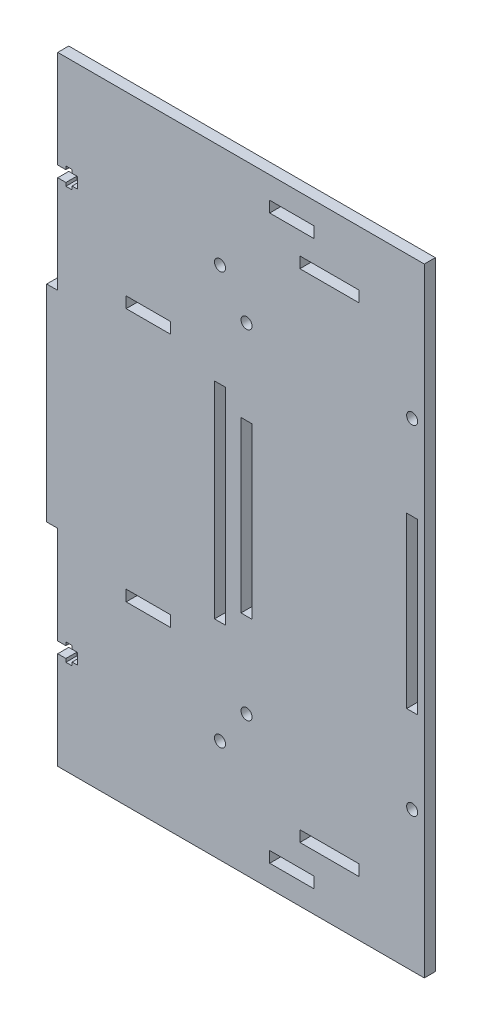
SolidWorks part; units mm, degrees
ref_plane "Alzado" through (0, 0, 0) normal (0, 0, 1) x (1, 0, 0)
ref_plane "Planta" through (0, 0, 0) normal (0, 1, 0) x (1, 0, 0)
ref_plane "Vista lateral" through (0, 0, 0) normal (1, 0, 0) x (0, 0, -1)
sketch "Croquis1" plane through (0, 0, 0) normal (0, 0, 1) x (1, 0, 0)
  line L0 (68, 280) -> (68, 236.7398) construction
  line L1 (0, 0) -> (136, 0)
  line L2 (0, 0) -> (0, 280)
  line L3 (0, 280) -> (136, 280)
  line L4 (136, 0) -> (136, 280)
  line L5 (0, 280) -> (5, 280)
  line L6 (0, 280) -> (0, 0)
  line L7 (0, 0) -> (5, 0)
  line L8 (5, 280) -> (5, 0)
  line L9 (131, 280) -> (131, 0)
  line L10 (0, 186.6667) -> (5, 186.6667)
  line L11 (5, 93.3333) -> (0, 93.3333)
  line L12 (131, 93.3333) -> (136, 93.3333)
  line L13 (136, 186.6667) -> (131, 186.6667)
  line L14 (0, 140) -> (16.4555, 140) construction
  dimension "D1" = 280
  dimension "D2" = 136
  dimension "D3" = 5
  dimension "D4" = 93.3333
  dimension "D5" = 93.3333
extrude "Saliente-Extruir1" add sketch "Croquis1" along normal blind 5 contours L9 L3 L8 L1 | L11 L8 L10 L6
sketch "Croquis2" plane through (0, 0, 5) normal (0, 0, 1) x (1, 0, 0)
  line L0 (5, 233.3333) -> (14, 233.3333) construction
  line L1 (5, 280) -> (5, 186.6667) construction
  line L2 (68, 280) -> (68, 267.6992)
  line L3 (5, 280) -> (131, 280) construction
  line L4 (0, 140) -> (9.7749, 140)
  line L5 (0, 93.3333) -> (0, 186.6667) construction
  line L6 (5, 235.8333) -> (8.7, 235.8333)
  line L7 (8.7, 235.8333) -> (8.7, 237.3333)
  line L8 (8.7, 237.3333) -> (11.5, 237.3333)
  line L9 (11.5, 237.3333) -> (11.5, 235.8333)
  line L10 (11.5, 235.8333) -> (14, 235.8333)
  line L11 (14, 235.8333) -> (14, 230.8333)
  line L12 (11.5, 230.8333) -> (14, 230.8333)
  line L13 (11.5, 229.3333) -> (11.5, 230.8333)
  line L14 (8.7, 229.3333) -> (11.5, 229.3333)
  line L15 (8.7, 230.8333) -> (8.7, 229.3333)
  line L16 (5, 230.8333) -> (8.7, 230.8333)
  line L17 (131, 233.3333) -> (122, 233.3333) construction
  line L18 (131, 230.8333) -> (127.3, 230.8333)
  line L19 (127.3, 230.8333) -> (127.3, 229.3333)
  line L20 (127.3, 229.3333) -> (124.5, 229.3333)
  line L21 (124.5, 229.3333) -> (124.5, 230.8333)
  line L22 (124.5, 230.8333) -> (122, 230.8333)
  line L23 (122, 235.8333) -> (122, 230.8333)
  line L24 (124.5, 235.8333) -> (122, 235.8333)
  line L25 (124.5, 237.3333) -> (124.5, 235.8333)
  line L26 (127.3, 237.3333) -> (124.5, 237.3333)
  line L27 (127.3, 235.8333) -> (127.3, 237.3333)
  line L28 (131, 235.8333) -> (127.3, 235.8333)
  line L29 (131, 46.6667) -> (122, 46.6667) construction
  line L30 (5, 46.6667) -> (14, 46.6667) construction
  line L31 (131, 44.1667) -> (127.3, 44.1667)
  line L32 (127.3, 44.1667) -> (127.3, 42.6667)
  line L33 (127.3, 42.6667) -> (124.5, 42.6667)
  line L34 (124.5, 42.6667) -> (124.5, 44.1667)
  line L35 (124.5, 44.1667) -> (122, 44.1667)
  line L36 (122, 44.1667) -> (122, 49.1667)
  line L37 (124.5, 49.1667) -> (122, 49.1667)
  line L38 (124.5, 50.6667) -> (124.5, 49.1667)
  line L39 (127.3, 50.6667) -> (124.5, 50.6667)
  line L40 (127.3, 49.1667) -> (127.3, 50.6667)
  line L41 (131, 49.1667) -> (127.3, 49.1667)
  line L42 (5, 49.1667) -> (8.7, 49.1667)
  line L43 (8.7, 49.1667) -> (8.7, 50.6667)
  line L44 (8.7, 50.6667) -> (11.5, 50.6667)
  line L45 (11.5, 50.6667) -> (11.5, 49.1667)
  line L46 (11.5, 49.1667) -> (14, 49.1667)
  line L47 (14, 44.1667) -> (14, 49.1667)
  line L48 (11.5, 44.1667) -> (14, 44.1667)
  line L49 (11.5, 42.6667) -> (11.5, 44.1667)
  line L50 (8.7, 42.6667) -> (11.5, 42.6667)
  line L51 (8.7, 44.1667) -> (8.7, 42.6667)
  line L52 (5, 44.1667) -> (8.7, 44.1667)
  line M12 (5, 280) -> (5, 186.6667)
  line M16 (5, 93.3333) -> (5, 0)
  dimension "D1" = 2.5
  dimension "D2" = 4
  dimension "D3" = 2.8
  dimension "D4" = 9
  dimension "D5" = 3.7
extrude "Cortar-Extruir1" cut sketch "Croquis2" against normal blind 5 contours L16 L15 L14 L13 L12 L11 L10 L9 L8 L7 L6 M12 | L52 L51 L50 L49 L48 L47 L46 L45 L44 L43 L42 M16
sketch "Croquis3" plane through (0, 0, 5) normal (0, 0, 1) x (1, 0, 0)
  line L0 (5, 280) -> (131, 280) construction
  line L1 (76, 280) -> (81, 280)
  line L2 (76, 280) -> (76, 0)
  line L3 (76, 0) -> (81, 0)
  line L4 (81, 280) -> (81, 0)
  line L5 (5, 0) -> (131, 0) construction
  line L6 (5, 280) -> (5, 235.8333) construction
  line L7 (76, 186.6667) -> (81, 186.6667)
  line L8 (76, 93.3333) -> (81, 93.3333)
  point P10 (5, 257.9167)
  point P13 (78.5, 186.6667)
  dimension "D1" = 71
  dimension "D2" = 5
  dimension "D3" = 93.3333
  dimension "D4" = 93.3333
extrude "Cortar-Extruir2" cut sketch "Croquis3" against normal blind 5 contours L2 L8 L4 L7
sketch "Croquis4" plane through (0, 0, 5) normal (0, 0, 1) x (1, 0, 0)
  line L0 (78.5, 186.6667) -> (78.5, 280) construction
  line L1 (76, 186.6667) -> (81, 186.6667) construction
  line L2 (5, 280) -> (131, 280) construction
  line L3 (78.5, 93.3333) -> (78.5, 0) construction
  line L5 (76, 93.3333) -> (81, 93.3333) construction
  line L6 (5, 0) -> (131, 0) construction
  circle A0 centre (78.5, 233.3333) radius 2.5
  circle A1 centre (78.5, 46.6667) radius 2.5
  dimension "D1" = 5
extrude "Cortar-Extruir3" cut sketch "Croquis4" against normal blind 5
sketch "Croquis5" plane through (0, 0, 5) normal (0, 0, 1) x (1, 0, 0)
  line L0 (76, 280) -> (76, 0) construction
  line L1 (76, 186.6667) -> (76, 93.3333) construction
  line L2 (5, 0) -> (131, 0) construction
  line L3 (76, 140) -> (83.8361, 140) construction
  line L4 (76, 200) -> (36, 200)
  line L5 (76, 200) -> (76, 195)
  line L6 (76, 195) -> (36, 195)
  line L7 (36, 200) -> (36, 195)
  line L8 (0, 93.3333) -> (0, 186.6667) construction
  line L9 (76, 270) -> (121, 270)
  line L10 (76, 270) -> (76, 265)
  line L11 (76, 265) -> (121, 265)
  line L12 (121, 270) -> (121, 265)
  line L13 (56, 195) -> (56, 200)
  line L14 (101, 270) -> (101, 265)
  line L15 (101, 10) -> (101, 15)
  line L16 (56, 85) -> (56, 80)
  line L17 (121, 10) -> (121, 15)
  line L18 (76, 15) -> (121, 15)
  line L19 (76, 10) -> (76, 15)
  line L20 (76, 10) -> (121, 10)
  line L21 (36, 80) -> (36, 85)
  line L22 (76, 85) -> (36, 85)
  line L23 (76, 80) -> (76, 85)
  line L24 (76, 80) -> (36, 80)
  point P7 (76, 140)
  point P21 (0, 140)
  point P24 (101, 267.5)
  dimension "D1" = 5
  dimension "D2" = 5
  dimension "D3" = 60
  dimension "D4" = 45
  dimension "D5" = 40
  dimension "D6" = 70
  dimension "D7" = 20
extrude "Cortar-Extruir4" cut sketch "Croquis5" against normal blind 5
sketch "Croquis6" plane through (0, 0, 5) normal (0, 0, 1) x (1, 0, 0)
  line L0 (5, 0) -> (131, 0) construction
  line L1 (131, 280) -> (171, 280)
  line L2 (131, 280) -> (131, 0)
  line L3 (131, 0) -> (171, 0)
  line L4 (171, 280) -> (171, 0)
  dimension "D1" = 40
extrude "Saliente-Extruir2" add sketch "Croquis6" against normal blind 5
sketch "Croquis7" plane through (0, 0, 5) normal (0, 0, 1) x (1, 0, 0)
  line L0 (93, 250) -> (93, 30)
  line L1 (93, 30) -> (163, 30)
  line L2 (163, 30) -> (163, 250)
  line L3 (163, 250) -> (93, 250)
  line L4 (88, 255) -> (88, 25)
  line L5 (88, 25) -> (168, 25)
  line L6 (168, 25) -> (168, 255)
  line L7 (168, 255) -> (88, 255)
  line L8 (5, 0) -> (171, 0) construction
  line L9 (81, 186.6667) -> (81, 93.3333) construction
  line L10 (93, 250) -> (93, 255)
  line L11 (93, 30) -> (93, 25)
  line L12 (163, 30) -> (163, 25)
  line L13 (163, 250) -> (163, 255)
  line L14 (5, 280) -> (171, 280) construction
  line L16 (88, 178.3333) -> (93, 178.3333)
  line L17 (93, 101.6667) -> (88, 101.6667)
  line L18 (163, 178.3333) -> (168, 178.3333)
  line L19 (163, 101.6667) -> (168, 101.6667)
  line L20 (88, 216.6667) -> (93, 216.6667) construction
  line L21 (128, 255) -> (128, 151.4654) construction
  line L22 (163, 140) -> (153.4822, 140) construction
  line L23 (114.6667, 255) -> (114.6667, 250)
  line L24 (141.3333, 255) -> (141.3333, 250)
  line L25 (141.3333, 25) -> (141.3333, 30)
  line L26 (114.6667, 25) -> (114.6667, 30)
  circle A0 centre (90.5, 216.6667) radius 2.5
  circle A1 centre (165.5, 216.6667) radius 2.5
  circle A2 centre (165.5, 63.3333) radius 2.5
  circle A3 centre (90.5, 63.3333) radius 2.5
  dimension "D9" = 5
  dimension "D2" = 70
  dimension "D4" = 30
  dimension "D5" = 12
  dimension "D6" = 76.6667
  dimension "D7" = 76.6667
  dimension "D8" = 38.3333
  dimension "D10" = 26.6667
  dimension "D11" = 26.6667
  dimension "D12" = 30
  dimension "D3" = 5
extrude "Cortar-Extruir5" cut sketch "Croquis7" against normal blind 5 contours L17 L0 L16 L4 | L2 L19 L6 L18 | L26 L5 L25 L1 | L24 L7 L23 L3 | A0 | A1 | A2 | A3
sketch "Croquis8" plane through (0, 0, 5) normal (0, 0, 1) x (1, 0, 0)
  line L0 (101, 10) -> (121, 10) construction
  line L1 (121, 10) -> (121, 15) construction
  line L2 (101, 15) -> (121, 15) construction
  line L3 (101, 10) -> (101, 15) construction
  line L4 (141.3333, 25) -> (141.3333, 30) construction
  line L5 (114.6667, 25) -> (141.3333, 25) construction
  line L6 (114.6667, 25) -> (114.6667, 30) construction
  line L7 (114.6667, 30) -> (141.3333, 30) construction
  line L8 (163, 101.6667) -> (168, 101.6667) construction
  line L9 (168, 101.6667) -> (168, 178.3333) construction
  line L10 (163, 178.3333) -> (168, 178.3333) construction
  line L11 (163, 101.6667) -> (163, 178.3333) construction
  line L12 (88, 178.3333) -> (93, 178.3333) construction
  line L13 (93, 178.3333) -> (93, 101.6667) construction
  line L14 (93, 101.6667) -> (88, 101.6667) construction
  line L15 (88, 178.3333) -> (88, 101.6667) construction
  line L16 (76, 93.3333) -> (81, 93.3333) construction
  line L17 (76, 186.6667) -> (81, 186.6667) construction
  line L18 (81, 186.6667) -> (81, 93.3333) construction
  line L19 (76, 186.6667) -> (76, 93.3333) construction
  line L20 (56, 85) -> (56, 80) construction
  line L21 (36, 80) -> (36, 85) construction
  line L22 (56, 80) -> (36, 80) construction
  line L23 (56, 85) -> (36, 85) construction
  line L24 (101, 270) -> (101, 265) construction
  line L25 (101, 270) -> (121, 270) construction
  line L26 (121, 270) -> (121, 265) construction
  line L27 (101, 265) -> (121, 265) construction
  line L28 (141.3333, 255) -> (141.3333, 250) construction
  line L29 (141.3333, 250) -> (114.6667, 250) construction
  line L30 (141.3333, 255) -> (114.6667, 255) construction
  line L31 (114.6667, 255) -> (114.6667, 250) construction
  line L32 (5, 93.3333) -> (5, 49.1667)
  line L33 (5, 49.1667) -> (8.7, 49.1667)
  line L34 (8.7, 49.1667) -> (8.7, 50.6667)
  line L35 (8.7, 50.6667) -> (11.5, 50.6667)
  line L36 (11.5, 50.6667) -> (11.5, 49.1667)
  line L37 (11.5, 49.1667) -> (14, 49.1667)
  line L38 (14, 49.1667) -> (14, 44.1667)
  line L39 (14, 44.1667) -> (11.5, 44.1667)
  line L40 (11.5, 44.1667) -> (11.5, 42.6667)
  line L41 (11.5, 42.6667) -> (8.7, 42.6667)
  line L42 (8.7, 42.6667) -> (8.7, 44.1667)
  line L43 (8.7, 44.1667) -> (5, 44.1667)
  line L44 (5, 44.1667) -> (5, 0)
  line L45 (5, 0) -> (171, 0)
  line L46 (171, 0) -> (171, 280)
  line L47 (171, 280) -> (5, 280)
  line L48 (5, 280) -> (5, 235.8333)
  line L49 (5, 235.8333) -> (8.7, 235.8333)
  line L50 (8.7, 235.8333) -> (8.7, 237.3333)
  line L51 (8.7, 237.3333) -> (11.5, 237.3333)
  line L52 (11.5, 237.3333) -> (11.5, 235.8333)
  line L53 (11.5, 235.8333) -> (14, 235.8333)
  line L54 (14, 235.8333) -> (14, 230.8333)
  line L55 (14, 230.8333) -> (11.5, 230.8333)
  line L56 (11.5, 230.8333) -> (11.5, 229.3333)
  line L57 (11.5, 229.3333) -> (8.7, 229.3333)
  line L58 (8.7, 229.3333) -> (8.7, 230.8333)
  line L59 (8.7, 230.8333) -> (5, 230.8333)
  line L60 (5, 230.8333) -> (5, 186.6667)
  line L61 (5, 186.6667) -> (0, 186.6667)
  line L62 (0, 186.6667) -> (0, 93.3333)
  line L63 (0, 93.3333) -> (5, 93.3333)
  line L64 (5, 93.3333) -> (5, 49.1667)
  line L65 (5, 49.1667) -> (8.7, 49.1667)
  line L66 (8.7, 49.1667) -> (8.7, 50.6667)
  line L67 (8.7, 50.6667) -> (11.5, 50.6667)
  line L68 (11.5, 50.6667) -> (11.5, 49.1667)
  line L69 (11.5, 49.1667) -> (14, 49.1667)
  line L70 (14, 49.1667) -> (14, 44.1667)
  line L71 (14, 44.1667) -> (11.5, 44.1667)
  line L72 (11.5, 44.1667) -> (11.5, 42.6667)
  line L73 (11.5, 42.6667) -> (8.7, 42.6667)
  line L74 (8.7, 42.6667) -> (8.7, 44.1667)
  line L75 (8.7, 44.1667) -> (5, 44.1667)
  line L76 (5, 44.1667) -> (5, 0)
  line L77 (5, 0) -> (171, 0)
  line L78 (171, 0) -> (171, 280)
  line L79 (171, 280) -> (5, 280)
  line L80 (5, 280) -> (5, 235.8333)
  line L81 (5, 235.8333) -> (8.7, 235.8333)
  line L82 (8.7, 235.8333) -> (8.7, 237.3333)
  line L83 (8.7, 237.3333) -> (11.5, 237.3333)
  line L84 (11.5, 237.3333) -> (11.5, 235.8333)
  line L85 (11.5, 235.8333) -> (14, 235.8333)
  line L86 (14, 235.8333) -> (14, 230.8333)
  line L87 (14, 230.8333) -> (11.5, 230.8333)
  line L88 (11.5, 230.8333) -> (11.5, 229.3333)
  line L89 (11.5, 229.3333) -> (8.7, 229.3333)
  line L90 (8.7, 229.3333) -> (8.7, 230.8333)
  line L91 (8.7, 230.8333) -> (5, 230.8333)
  line L92 (5, 230.8333) -> (5, 186.6667)
  line L93 (5, 186.6667) -> (0, 186.6667)
  line L94 (0, 186.6667) -> (0, 93.3333)
  line L95 (0, 93.3333) -> (5, 93.3333)
  line L96 (56, 195) -> (56, 200) construction
  line L97 (56, 195) -> (36, 195) construction
  line L98 (36, 200) -> (36, 195) construction
  line L99 (56, 200) -> (36, 200) construction
  line L100 (101, 10) -> (121, 10)
  line L101 (121, 10) -> (121, 15)
  line L102 (101, 15) -> (121, 15)
  line L103 (101, 10) -> (101, 15)
  line L104 (141.3333, 25) -> (141.3333, 30)
  line L105 (114.6667, 25) -> (141.3333, 25)
  line L106 (114.6667, 25) -> (114.6667, 30)
  line L107 (114.6667, 30) -> (141.3333, 30)
  line L108 (163, 101.6667) -> (168, 101.6667)
  line L109 (168, 101.6667) -> (168, 178.3333)
  line L110 (163, 178.3333) -> (168, 178.3333)
  line L111 (163, 101.6667) -> (163, 178.3333)
  line L112 (88, 178.3333) -> (93, 178.3333)
  line L113 (93, 178.3333) -> (93, 101.6667)
  line L114 (93, 101.6667) -> (88, 101.6667)
  line L115 (88, 178.3333) -> (88, 101.6667)
  line L116 (76, 93.3333) -> (81, 93.3333)
  line L117 (76, 186.6667) -> (81, 186.6667)
  line L118 (81, 186.6667) -> (81, 93.3333)
  line L119 (76, 186.6667) -> (76, 93.3333)
  line L120 (56, 85) -> (56, 80)
  line L121 (36, 80) -> (36, 85)
  line L122 (56, 80) -> (36, 80)
  line L123 (56, 85) -> (36, 85)
  line L124 (101, 270) -> (101, 265)
  line L125 (101, 270) -> (121, 270)
  line L126 (121, 270) -> (121, 265)
  line L127 (101, 265) -> (121, 265)
  line L128 (141.3333, 255) -> (141.3333, 250)
  line L129 (141.3333, 250) -> (114.6667, 250)
  line L130 (141.3333, 255) -> (114.6667, 255)
  line L131 (114.6667, 255) -> (114.6667, 250)
  line L132 (56, 195) -> (56, 200)
  line L133 (56, 195) -> (36, 195)
  line L134 (36, 200) -> (36, 195)
  line L135 (56, 200) -> (36, 200)
  circle A0 centre (165.5, 63.3333) radius 2.5 construction
  circle A1 centre (90.5, 63.3333) radius 2.5 construction
  circle A2 centre (78.5, 46.6667) radius 2.5 construction
  circle A3 centre (165.5, 216.6667) radius 2.5 construction
  circle A4 centre (90.5, 216.6667) radius 2.5 construction
  circle A5 centre (78.5, 233.3333) radius 2.5 construction
  circle A6 centre (165.5, 63.3333) radius 2.5
  circle A7 centre (90.5, 63.3333) radius 2.5
  circle A8 centre (78.5, 46.6667) radius 2.5
  circle A9 centre (165.5, 216.6667) radius 2.5
  circle A10 centre (90.5, 216.6667) radius 2.5
  circle A11 centre (78.5, 233.3333) radius 2.5
  dimension "D1" = 0
